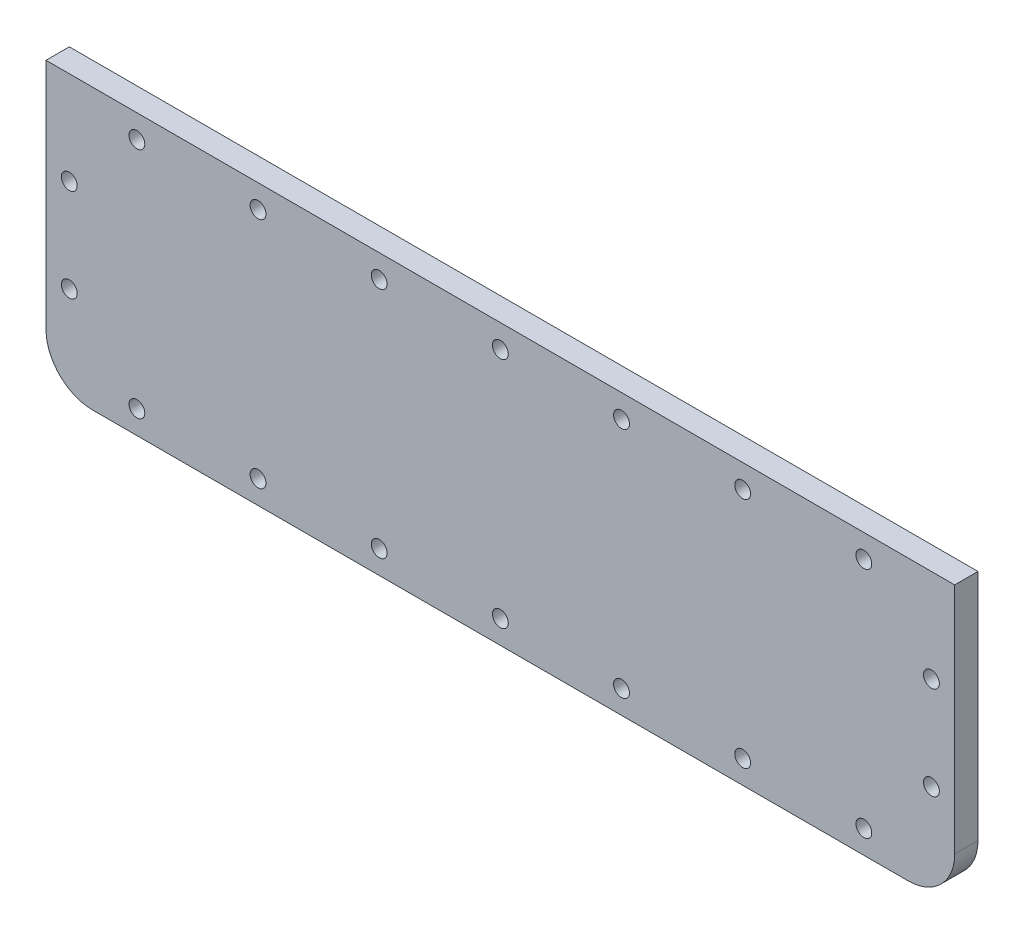
SolidWorks part; units mm, degrees
material "Acrylic (Medium-high impact)"
ref_plane "Front Plane" through (0, 0, 0) normal (0, 0, 1) x (1, 0, 0)
ref_plane "Top Plane" through (0, 0, 0) normal (0, 1, 0) x (1, 0, 0)
ref_plane "Right Plane" through (0, 0, 0) normal (1, 0, 0) x (0, 0, -1)
sketch "Sketch1" plane through (0, 0, 0) normal (0, 0, 1) x (1, 0, 0)
  line L1 (-123.825, 38.1) -> (123.825, 38.1)
  line L2 (-123.825, 38.1) -> (-123.825, -38.1)
  line L3 (-123.825, -38.1) -> (123.825, -38.1)
  line L4 (123.825, 38.1) -> (123.825, -38.1)
  line L5 (-123.825, 38.1) -> (123.825, -38.1) construction
  line L6 (-123.825, -38.1) -> (123.825, 38.1) construction
  circle A0 centre (-117.475, 12.7) radius 2.159 construction
  circle A1 centre (-117.475, -12.7) radius 2.159 construction
  circle A2 centre (-99.06, -31.75) radius 2.159 construction
  circle A3 centre (-66.04, -31.75) radius 2.159 construction
  circle A4 centre (-33.02, -31.75) radius 2.159 construction
  circle A5 centre (0, -31.75) radius 2.159 construction
  circle A6 centre (33.02, -31.75) radius 2.159 construction
  circle A7 centre (66.04, -31.75) radius 2.159 construction
  circle A8 centre (99.06, -31.75) radius 2.159 construction
  circle A9 centre (117.475, -12.7) radius 2.159 construction
  circle A10 centre (117.475, 12.7) radius 2.159 construction
  circle A11 centre (99.06, 31.75) radius 2.159 construction
  circle A12 centre (66.04, 31.75) radius 2.159 construction
  circle A13 centre (33.02, 31.75) radius 2.159 construction
  circle A14 centre (0, 31.75) radius 2.159 construction
  circle A15 centre (-33.02, 31.75) radius 2.159 construction
  circle A16 centre (-66.04, 31.75) radius 2.159 construction
  circle A17 centre (-99.06, 31.75) radius 2.159 construction
  circle A18 centre (-117.475, 12.7) radius 2.159
  circle A19 centre (-117.475, -12.7) radius 2.159
  circle A20 centre (-99.06, -31.75) radius 2.159
  circle A21 centre (-66.04, -31.75) radius 2.159
  circle A22 centre (-33.02, -31.75) radius 2.159
  circle A23 centre (0, -31.75) radius 2.159
  circle A24 centre (33.02, -31.75) radius 2.159
  circle A25 centre (66.04, -31.75) radius 2.159
  circle A26 centre (99.06, -31.75) radius 2.159
  circle A27 centre (117.475, -12.7) radius 2.159
  circle A28 centre (117.475, 12.7) radius 2.159
  circle A29 centre (99.06, 31.75) radius 2.159
  circle A30 centre (66.04, 31.75) radius 2.159
  circle A31 centre (33.02, 31.75) radius 2.159
  circle A32 centre (0, 31.75) radius 2.159
  circle A33 centre (-33.02, 31.75) radius 2.159
  circle A34 centre (-66.04, 31.75) radius 2.159
  circle A35 centre (-99.06, 31.75) radius 2.159
  point P0 (0, 0)
  dimension "D1" = 76.2
  dimension "D2" = 247.65
extrude "Boss-Extrude1" add sketch "Sketch1" along normal blind 6.35
fillet "Fillet1" radius 12.7 2 edges at (123.825, -38.1, 3.175) (-123.825, -38.1, 3.175)
